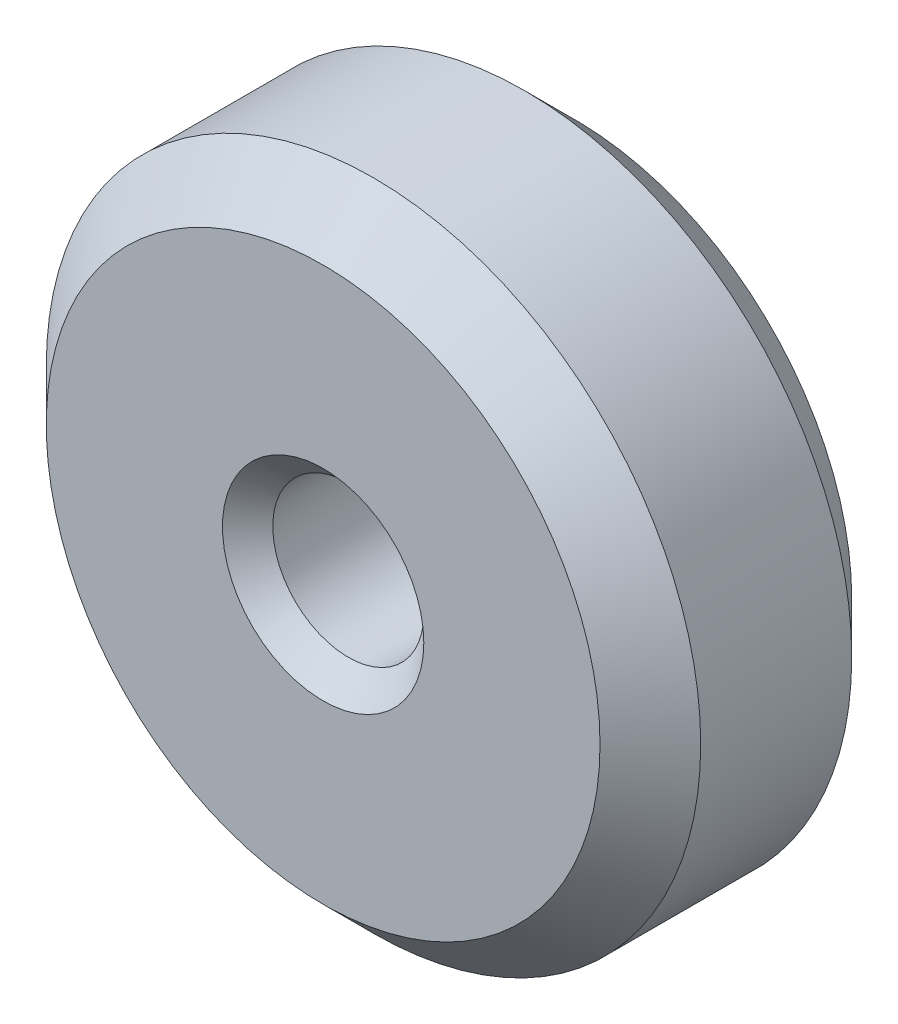
SolidWorks part; units mm, degrees
ref_plane "前视基准面" through (0, 0, 0) normal (0, 0, 1) x (1, 0, 0)
ref_plane "上视基准面" through (0, 0, 0) normal (0, 1, 0) x (1, 0, 0)
ref_plane "右视基准面" through (0, 0, 0) normal (1, 0, 0) x (0, 0, -1)
sketch "草图1" plane through (0, 0, 0) normal (0, 0, 1) x (1, 0, 0)
  circle A0 centre (0, 0) radius 6.5
  circle A1 centre (0, 0) radius 1.5
  dimension "D1" = 3
  dimension "D2" = 13
extrude "凸台-拉伸1" add sketch "草图1" along normal blind 5
chamfer "倒角1" distance 1 angle 45 2 edges at (6.5, 0, 0) (6.5, 0, 5)
chamfer "倒角2" distance 0.5 angle 45 2 edges at (1.5, 0, 0) (1.5, 0, 5)
